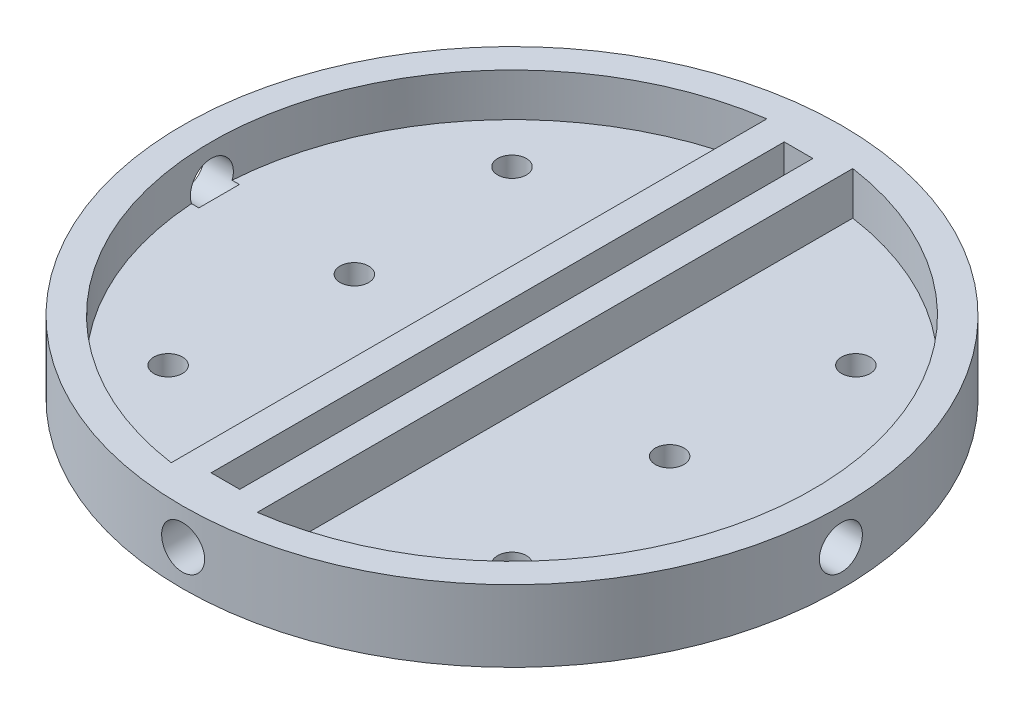
SolidWorks part; units mm, degrees
material "ABS"
ref_plane "Front Plane" through (0, 0, 0) normal (0, 0, 1) x (1, 0, 0)
ref_plane "Top Plane" through (0, 0, 0) normal (0, 1, 0) x (1, 0, 0)
ref_plane "Right Plane" through (0, 0, 0) normal (1, 0, 0) x (0, 0, -1)
sketch "Sketch17" plane through (0, 0, 0) normal (0, 0, 1) x (1, 0, 0)
  line L0 (0, 36.6652) -> (0, -18.0015)
sketch "Sketch5" plane through (0, 0, 0) normal (0, 1, 0) x (1, 0, 0)
  circle A0 centre (0, 0) radius 73.025
  circle A1 centre (38.1, 38.1) radius 3.175
  circle A2 centre (38.1, -38.1) radius 3.175
  circle A3 centre (-38.1, 38.1) radius 3.175
  circle A4 centre (-38.1, -38.1) radius 3.175
extrude "PlateBase" add sketch "Sketch5" along normal blind 6.35
sketch "Sketch6" plane through (0, 6.35, 0) normal (0, 1, 0) x (1, 0, 0)
  line L1 (3.175, 0) -> (3.175, 72.9559)
  line L3 (3.175, 0) -> (3.175, -72.9559)
  line L4 (0, 0) -> (3.175, 0)
  line L5 (-3.175, 0) -> (-3.175, 72.9559)
  line L6 (-9.525, 0) -> (-9.525, 72.4011)
  line L7 (-9.525, 0) -> (-9.525, -72.4011)
  line L8 (-3.175, 0) -> (-3.175, -72.9559)
  line L9 (9.525, 0) -> (9.525, 72.4011)
  line L10 (9.525, 0) -> (9.525, -72.4011)
  circle A0 centre (0, 0) radius 73.025 construction
  circle M4 centre (0, 0) radius 73.025
extrude "PlateTop" add sketch "Sketch6" along normal blind 9.525 contours L8 L5 L6 L7 M4 | L10 L9 L1 L3 M4
sketch "Sketch9" plane through (0, 6.35, 0) normal (0, 1, 0) x (1, 0, 0)
  circle A0 centre (0, 0) radius 66.675
  circle A1 centre (0, 0) radius 73.025
extrude "PlateWalls" add sketch "Sketch9" along normal blind 9.525
sketch "Sketch13" plane through (0, 6.35, 0) normal (0, 1, 0) x (1, 0, 0)
  circle A0 centre (34.925, 0) radius 3.175
extrude "RightThruHole" cut sketch "Sketch13" against normal blind 6.35
sketch "Sketch14" plane through (0, 6.35, 0) normal (0, 1, 0) x (1, 0, 0)
  circle A0 centre (-34.925, 0) radius 3.175
extrude "LeftThruHole" cut sketch "Sketch14" against normal blind 6.35
sketch "Sketch15" plane through (0, 6.35, 0) normal (0, 1, 0) x (1, 0, 0)
  line L1 (-3.175, 66.5994) -> (-3.175, -66.5994) construction
  line L2 (-3.175, 63.5) -> (3.175, 63.5)
  line L3 (3.175, -66.5994) -> (3.175, 66.5994) construction
  line L4 (3.175, 63.5) -> (3.175, 66.5994)
  line L5 (-3.175, 66.5994) -> (-3.175, 63.5)
  line L7 (-3.175, -63.5) -> (-3.175, -66.5994)
  line L8 (-3.175, -63.5) -> (3.175, -63.5)
  line L9 (3.175, -63.5) -> (3.175, -66.5994)
  arc A0 (3.175, 66.5994) -> (-3.175, 66.5994) centre (0, 0) ccw construction
  circle A1 centre (0, 0) radius 66.675 construction
  arc A2 (-3.175, 66.5994) -> (3.175, 66.5994) centre (0, 0) cw
  arc A3 (-3.175, -66.5994) -> (3.175, -66.5994) centre (0, 0) ccw
extrude "Boss-Extrude1" add sketch "Sketch15" along normal blind 9.525 from surface at 0 starting at face at (0, 6.35, 0)
sketch3d "3DSketch1" plane through (0, 0, 0) normal (0, 0, 1) x (1, 0, 0)
sketch "Sketch16" plane through (0, 0, 73.025) normal (0, 0, 1) x (1, 0, 0)
  line L0 (0, 0) -> (0, 7.9375)
  circle A0 centre (0, 7.9375) radius 4.765
extrude "InsertHole" cut sketch "Sketch16" against normal blind 8.128
pattern_circular "InsertHoles" count 4 over 360 about axis through (0, 0, 0) along (0, 1, 0) of "InsertHole"
